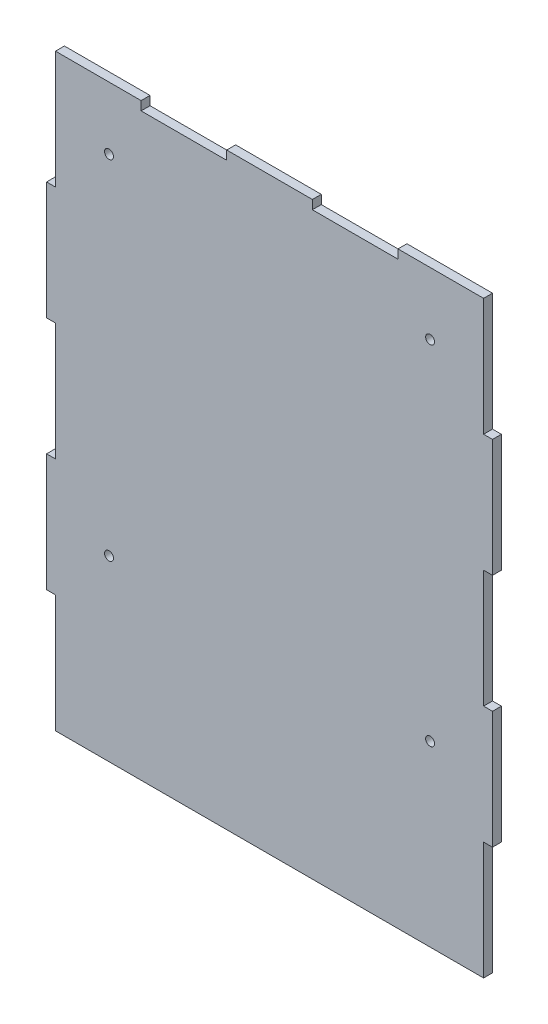
SolidWorks part; units mm, degrees
material "Contreplaqué pin"
ref_plane "Plan de face" through (0, 0, 0) normal (0, 0, 1) x (1, 0, 0)
ref_plane "Plan de dessus" through (0, 0, 0) normal (0, 1, 0) x (1, 0, 0)
ref_plane "Plan de droite" through (0, 0, 0) normal (1, 0, 0) x (0, 0, -1)
sketch "Esquisse1" plane through (0, 0, 0) normal (0, 0, 1) x (1, 0, 0)
  line L0 (0, 66) -> (5, 66)
  line L1 (5, 0) -> (245, 0)
  line L2 (0, 66) -> (0, 132)
  line L3 (5, 330) -> (53, 330)
  line L4 (250, 66) -> (250, 132)
  line L5 (5, 66) -> (5, 0)
  line L6 (0, 132) -> (5, 132)
  line L7 (5, 132) -> (5, 198)
  line L8 (5, 198) -> (0, 198)
  line L9 (5, 330) -> (5, 264)
  line L10 (5, 264) -> (0, 264)
  line L11 (0, 198) -> (0, 264)
  line L12 (250, 264) -> (245, 264)
  line L13 (245, 264) -> (245, 330)
  line L14 (250, 198) -> (245, 198)
  line L15 (245, 198) -> (245, 132)
  line L16 (245, 132) -> (250, 132)
  line L17 (250, 66) -> (245, 66)
  line L18 (245, 66) -> (245, 0)
  line L19 (250, 198) -> (250, 264)
  line L20 (53, 330) -> (53, 325)
  line L21 (53, 325) -> (101, 325)
  line L22 (101, 325) -> (101, 330)
  line L23 (149, 330) -> (149, 325)
  line L24 (149, 325) -> (197, 325)
  line L25 (197, 325) -> (197, 330)
  line L26 (101, 330) -> (149, 330)
  line L27 (197, 330) -> (245, 330)
  dimension "D1" = 250
  dimension "D2" = 330
  dimension "D3" = 5
  dimension "D4" = 5
  dimension "D5" = 5
extrude "Boss.-Extru.1" add sketch "Esquisse1" along normal blind 5
hole_wizard "Diamètre du perçage Ø5.0 (5)1" positions "Esquisse2" profile "Esquisse3" hole size "Ø5.0" standard "DIN" end condition up to next
sketch "Esquisse2" plane through (0, 0, 5) normal (0, 0, 1) x (1, 0, 0)
  line L0 (35, 295) -> (35, 100) construction
  line L1 (35, 100) -> (215, 100) construction
  line L2 (215, 100) -> (215, 295) construction
  line L3 (215, 295) -> (35, 295) construction
  line L5 (5, 198) -> (5, 132) construction
  line L6 (101, 325) -> (53, 325) construction
  line L7 (245, 132) -> (245, 198) construction
  line L8 (5, 0) -> (245, 0) construction
  point P0 (35, 295)
  point P2 (215, 295)
  point P4 (215, 100)
  point P6 (35, 100)
  dimension "D1" = 30
  dimension "D2" = 30
  dimension "D3" = 30
  dimension "D4" = 100
sketch "Esquisse3" plane through (35, 295, 5) normal (1, 0, 0) x (0, -1, 0)
  line L0 (0, 0) -> (0, 5)
  line L1 (0, 5) -> (2.5, 5)
  line L2 (2.5, 5) -> (2.5, 0)
  line L5 (2.5, 0) -> (0, 0)
  line L11 (0, -6.35) -> (0, 107.95) construction
  dimension "Diamètre du perçage jusqu'au prochain" = 5
  dimension "Profondeur du perçage jusqu'au prochain" = 5
